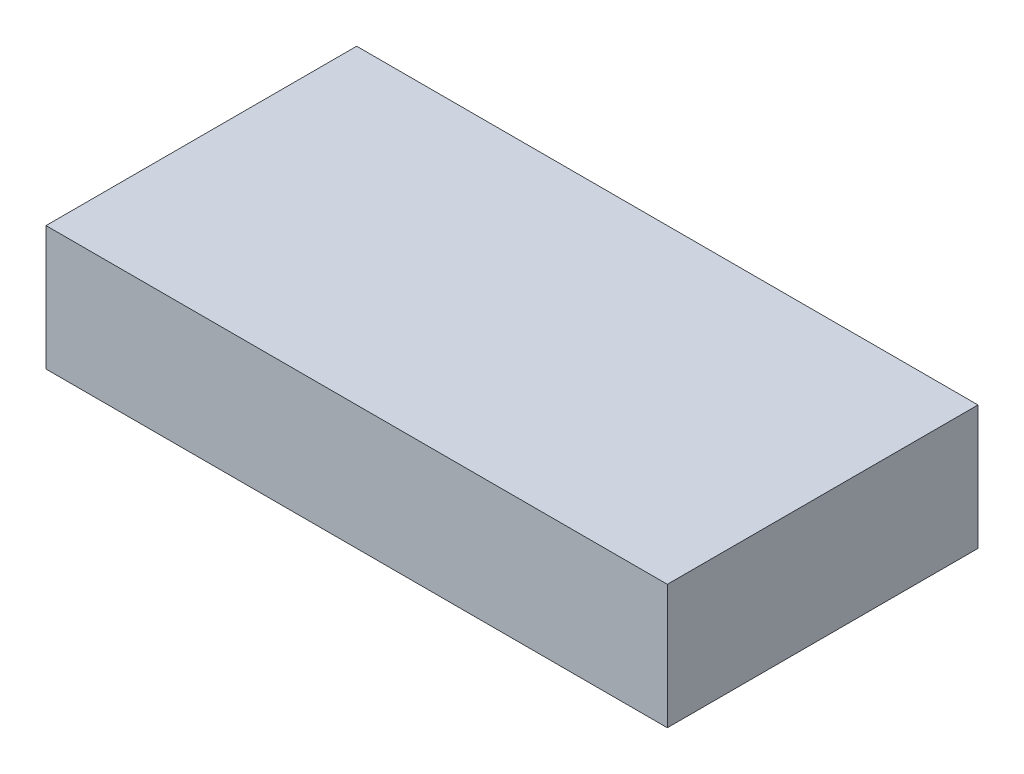
SolidWorks part; units mm, degrees
material "Epoxy, Unfilled"
ref_plane "Front Plane" through (0, 0, 0) normal (0, 0, 1) x (1, 0, 0)
ref_plane "Top Plane" through (0, 0, 0) normal (0, 1, 0) x (1, 0, 0)
ref_plane "Right Plane" through (0, 0, 0) normal (1, 0, 0) x (0, 0, -1)
sketch "Sketch1" plane through (0, 0, 0) normal (0, 1, 0) x (1, 0, 0)
  line L1 (0, 0) -> (10, 0)
  line L2 (0, 0) -> (0, 5)
  line L3 (0, 5) -> (10, 5)
  line L4 (10, 0) -> (10, 5)
  dimension "D1" = 5
  dimension "D2" = 10
extrude "Boss-Extrude1" add sketch "Sketch1" along normal blind 2
